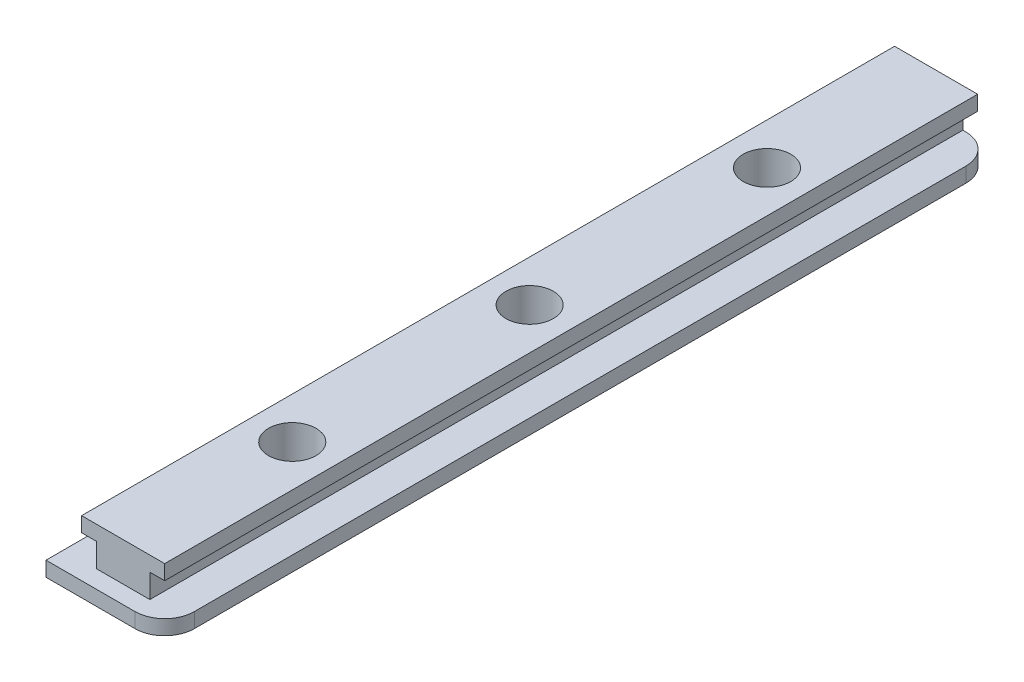
SolidWorks part; units mm, degrees
ref_plane "Front Plane" through (0, 0, 0) normal (0, 0, 1) x (1, 0, 0)
ref_plane "Top Plane" through (0, 0, 0) normal (0, 1, 0) x (1, 0, 0)
ref_plane "Right Plane" through (0, 0, 0) normal (1, 0, 0) x (0, 0, -1)
sketch "Sketch1" plane through (0, 0, 0) normal (0, 0, 1) x (1, 0, 0)
  line L0 (0, 4.5) -> (0, -4.5) construction
  line L1 (-7, 4.5) -> (7, 4.5)
  line L2 (-7, 4.5) -> (-7, 2)
  line L3 (-10, -4.5) -> (10, -4.5)
  line L5 (-10, -2) -> (-4.5, -2)
  line L6 (-4.5, -2) -> (-4.5, 2)
  line L7 (-4.5, 2) -> (-7, 2)
  line L8 (-10, -2) -> (-10, -4.5)
  line L27 (10, -2) -> (10, -4.5)
  line L28 (4.5, 2) -> (7, 2)
  line L29 (4.5, -2) -> (4.5, 2)
  line L30 (10, -2) -> (4.5, -2)
  line L31 (7, 4.5) -> (7, 2)
  point P0 (0, 0)
  dimension "D1" = 9
  dimension "D2" = 2.5
  dimension "D3" = 2.5
  dimension "D4" = 7
  dimension "D5" = 4.5
  dimension "D6" = 10
extrude "Boss-Extrude2" add sketch "Sketch1" along normal mid plane 137
sketch "Sketch4" plane through (0, 4.5, 0) normal (0, 1, 0) x (1, 0, 0)
  circle A0 centre (0, 0) radius 4
  circle A1 centre (0, 40) radius 4
  circle A2 centre (0, -40) radius 4
  dimension "D1" = 8
  dimension "D2" = 8
  dimension "D3" = 8
  dimension "D4" = 40
  dimension "D5" = 40
extrude "Cut-Extrude1" cut sketch "Sketch4" against normal blind 6
sketch "Sketch5" plane through (0, -1.5, 0) normal (0, 1, 0) x (1, 0, 0)
  circle A0 centre (0, 40) radius 2.5
  circle A1 centre (0, 0) radius 2.5
  circle A2 centre (0, -40) radius 2.5
  dimension "D1" = 5
extrude "Cut-Extrude2" cut sketch "Sketch5" against normal blind 4
sketch "Sketch7" plane through (0, 0, 68.5) normal (0, 0, 1) x (1, 0, 0)
  line L1 (-10, -2) -> (10, -2)
  line L2 (-10, -2) -> (-10, -4.5)
  line L3 (-10, -4.5) -> (10, -4.5)
  line L4 (10, -2) -> (10, -4.5)
extrude "Boss-Extrude6" add sketch "Sketch7" along normal blind 3
fillet "Fillet2" radius 5 2 edges at (10, -3.25, -68.5) (10, -3.25, 71.5)
